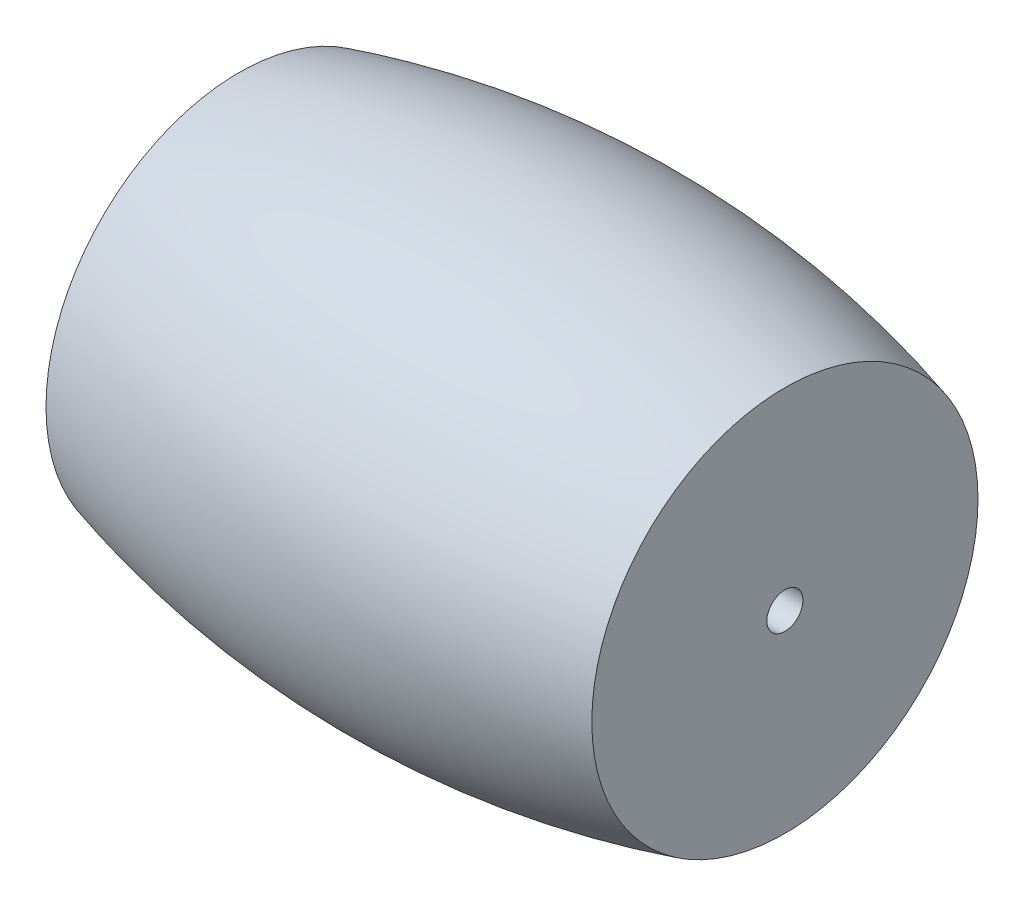
SolidWorks part; units mm, degrees
material "Nylon 101 20%"
ref_plane "Front Plane" through (0, 0, 0) normal (0, 0, 1) x (1, 0, 0)
ref_plane "Top Plane" through (0, 0, 0) normal (0, 1, 0) x (1, 0, 0)
ref_plane "Right Plane" through (0, 0, 0) normal (1, 0, 0) x (0, 0, -1)
sketch "Sketch2" plane through (0, 0, 0) normal (0, 0, 1) x (1, 0, 0)
  line L0 (-17.4164, 0) -> (-17.4164, 12.3221) construction
  line L1 (-17.4164, 1.15) -> (-17.4164, 12.3221)
  line L2 (28.7417, 0) -> (-28.7417, 0) construction
  line L3 (17.4164, 0) -> (-17.4164, 0) construction
  line L4 (17.4164, 0) -> (17.4164, 12.3221) construction
  line L5 (17.4164, 1.15) -> (17.4164, 12.3221)
  line L6 (-17.4164, 1.15) -> (17.4164, 1.15)
  circle A0 centre (0, -49.782) radius 64.5 construction
  arc A1 (17.4164, 12.3221) -> (-17.4164, 12.3221) centre (0, -49.782) ccw
  dimension "D1" = 1.15
revolve "Revolve2" add sketch "Sketch2" angle 360 about L3
